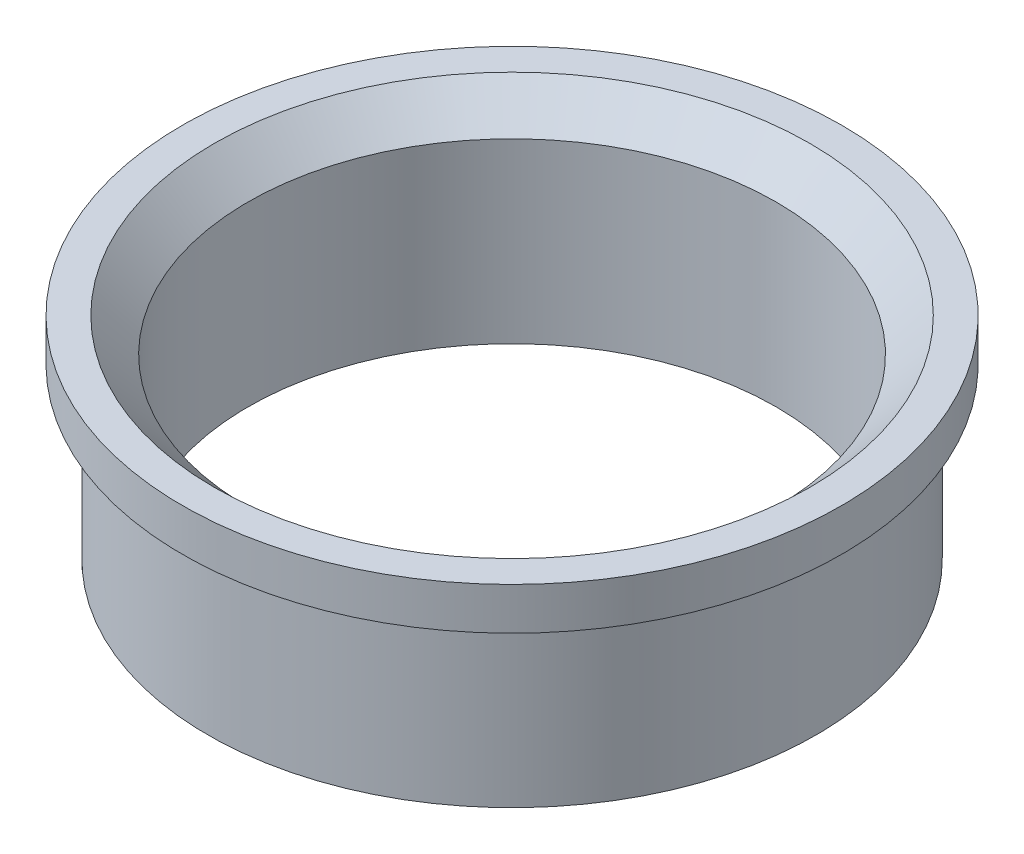
SolidWorks part; units mm, degrees
ref_plane "Front Plane" through (0, 0, 0) normal (0, 0, 1) x (1, 0, 0)
ref_plane "Top Plane" through (0, 0, 0) normal (0, 1, 0) x (1, 0, 0)
ref_plane "Right Plane" through (0, 0, 0) normal (1, 0, 0) x (0, 0, -1)
sketch "Sketch1" plane through (0, 0, 0) normal (0, 0, 1) x (1, 0, 0)
  line L0 (0, 0) -> (0, 73.2493) construction
  line L1 (62.5, 0) -> (62.5, 42)
  line L2 (62.5, 42) -> (70.5, 50)
  line L3 (70.5, 50) -> (78, 50)
  line L4 (78, 50) -> (78, 40)
  line L5 (78, 40) -> (72, 40)
  line L6 (72, 40) -> (72, 0)
  line L7 (72, 0) -> (62.5, 0)
  dimension "D1" = 144
  dimension "D2" = 156
  dimension "D3" = 141
  dimension "D4" = 40
  dimension "D5" = 10
  dimension "D6" = 135
  dimension "D7" = 8
revolve "Revolve1" add sketch "Sketch1" angle 360 about L0
